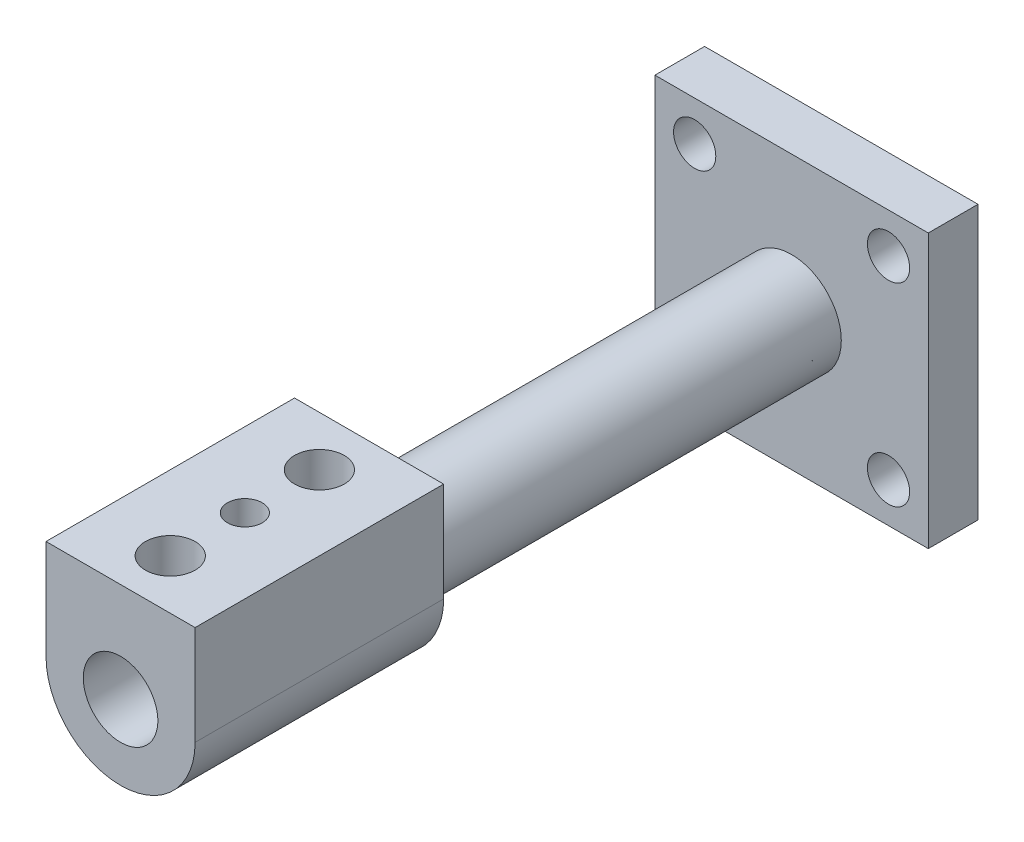
SolidWorks part; units mm, degrees
ref_plane "Front Plane" through (0, 0, 0) normal (0, 0, 1) x (1, 0, 0)
ref_plane "Top Plane" through (0, 0, 0) normal (0, 1, 0) x (1, 0, 0)
ref_plane "Right Plane" through (0, 0, 0) normal (1, 0, 0) x (0, 0, -1)
sketch "Sketch1" plane through (0, 0, 0) normal (0, 0, 1) x (1, 0, 0)
  line L1 (-27.5, 27.5) -> (27.5, 27.5)
  line L2 (-27.5, 27.5) -> (-27.5, -27.5)
  line L3 (-27.5, -27.5) -> (27.5, -27.5)
  line L4 (27.5, 27.5) -> (27.5, -27.5)
  line L5 (-27.5, 27.5) -> (27.5, -27.5) construction
  line L6 (-27.5, -27.5) -> (27.5, 27.5) construction
  point P0 (0, 0)
  dimension "D1" = 55
  dimension "D2" = 55
extrude "Boss-Extrude1" add sketch "Sketch1" along normal blind 10 contours L1 L4 L3 L2
sketch "Sketch2" plane through (0, 0, 10) normal (0, 0, 1) x (1, 0, 0)
  circle A0 centre (0, 0) radius 10
  dimension "D1" = 20
extrude "Boss-Extrude2" add sketch "Sketch2" along normal blind 85
sketch "Sketch3" plane through (0, 0, 95) normal (0, 0, 1) x (1, 0, 0)
  line L2 (-15, 0) -> (-15, 20)
  line L3 (-15, 20) -> (15, 20)
  line L4 (15, 0) -> (15, 20)
  arc A0 (-15, 0) -> (15, 0) centre (0, 0) ccw
  point P0 (0, 0)
  dimension "D3" = 30
  dimension "D1" = 30
extrude "Boss-Extrude3" add sketch "Sketch3" along normal blind 50
sketch "Sketch4" plane through (0, 0, 0) normal (0, 0, -1) x (-1, 0, 0)
  circle A0 centre (0, 0) radius 7.5
  dimension "D1" = 15
extrude "Cut-Extrude1" cut sketch "Sketch4" against normal through all both and the other way through all
sketch "Sketch5" plane through (0, 20, 0) normal (0, 1, 0) x (1, 0, 0)
  line L0 (15, -145) -> (-15, -145) construction
  line L1 (15, -95) -> (-15, -95) construction
  circle A0 centre (0, -135) radius 5
  circle A1 centre (0, -120) radius 3.5
  circle A2 centre (0, -105) radius 5
  dimension "D4" = 10
  dimension "D5" = 10
  dimension "D6" = 7
  dimension "D1" = 10
  dimension "D2" = 15
  dimension "D3" = 10
extrude "Cut-Extrude2" cut sketch "Sketch5" against normal up to next
sketch "Sketch6" plane through (0, 0, 10) normal (0, 0, 1) x (1, 0, 0)
  line L0 (-47.7539, 0) -> (61.1794, 0) construction
  line L1 (0, 48.214) -> (0, -53.4118) construction
  circle A0 centre (-19.5, 19.5) radius 4.25
  circle A1 centre (19.5, 19.5) radius 4.25
  circle A2 centre (19.5, -19.5) radius 4.25
  circle A3 centre (-19.5, -19.5) radius 4.25
  dimension "D1" = 8.5
  dimension "D2" = 39
  dimension "D3" = 39
extrude "Cut-Extrude3" cut sketch "Sketch6" against normal blind 50
